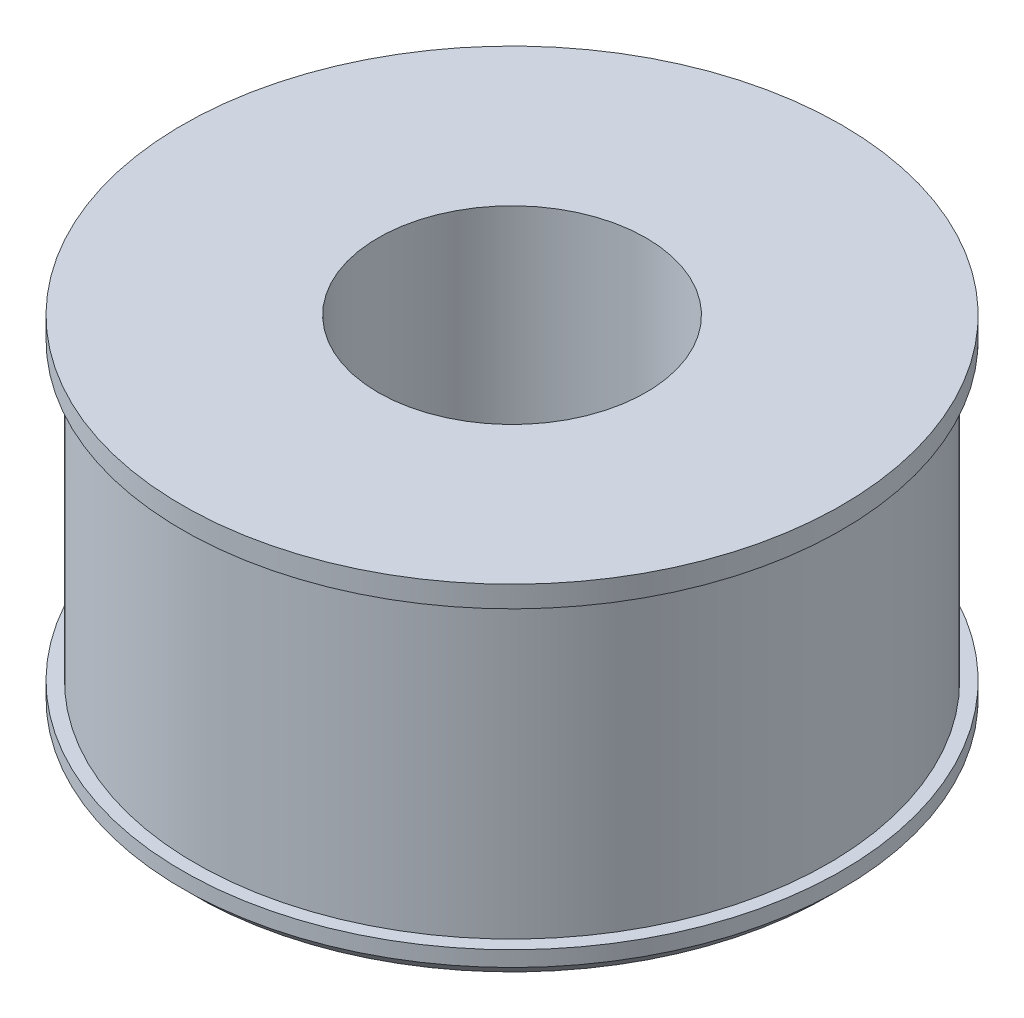
SolidWorks part; units mm, degrees
ref_plane "Alzado" through (0, 0, 0) normal (0, 0, 1) x (1, 0, 0)
ref_plane "Planta" through (0, 0, 0) normal (0, 1, 0) x (1, 0, 0)
ref_plane "Vista lateral" through (0, 0, 0) normal (1, 0, 0) x (0, 0, -1)
sketch "Croquis1" plane through (0, 0, 0) normal (1, 0, 0) x (0, 0, -1)
  line L0 (0, 0) -> (0, -66.5134) construction
  line L1 (0, -66.5134) -> (0, 82.3614) construction
  line L2 (54.2673, -66.5134) -> (128.2245, -66.5134)
  line L3 (128.2245, -66.5134) -> (128.2245, -60.2703)
  line L4 (128.2245, -60.2703) -> (128.2245, 59.3098)
  line L5 (128.2245, 59.3098) -> (133.5071, 59.3098)
  line L6 (133.5071, 59.3098) -> (133.5071, 67.9542)
  line L7 (133.5071, 67.9542) -> (54.2673, 67.9542)
  line L8 (54.2673, 67.9542) -> (54.2673, -66.5134)
  line L9 (128.2245, -60.2703) -> (133.5071, -60.2703)
  line L10 (133.5071, -60.2703) -> (133.5071, -66.5134)
  line L11 (133.5071, -66.5134) -> (128.2245, -71.7961)
  line L12 (128.2245, -71.7961) -> (128.2245, -60.2703)
revolve "Revolución1" add sketch "Croquis1" angle 360 about L1
